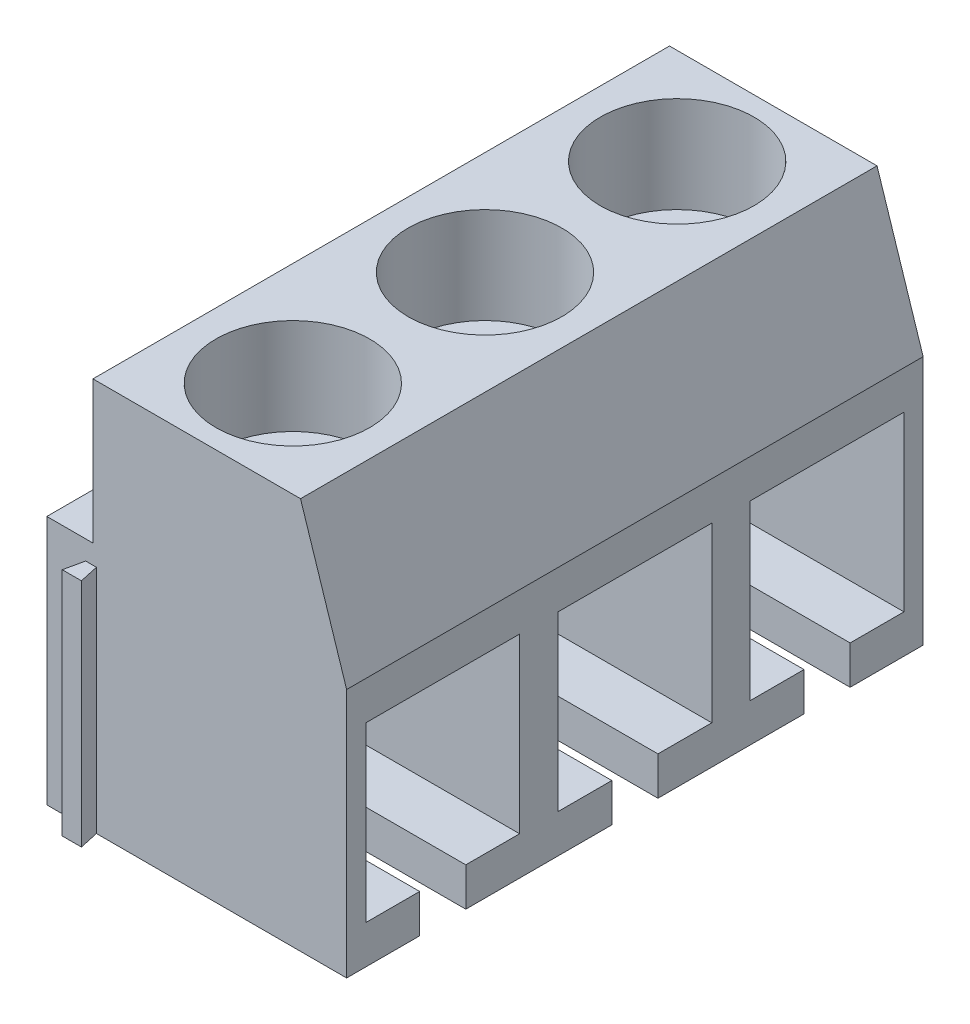
SolidWorks part; units mm, degrees
material "ABS"
ref_plane "Front Plane" through (0, 0, 0) normal (0, 0, 1) x (1, 0, 0)
ref_plane "Top Plane" through (0, 0, 0) normal (0, 1, 0) x (1, 0, 0)
ref_plane "Right Plane" through (0, 0, 0) normal (1, 0, 0) x (0, 0, -1)
sketch "Sketch1" plane through (0, 0, 0) normal (0, 0, 1) x (1, 0, 0)
  line L0 (-2.7, 5.1) -> (-2.7, 1.4)
  line L1 (-3.9, 5.1) -> (3.9, 5.1)
  line L2 (-3.9, 5.1) -> (-3.9, -5.1)
  line L3 (-3.9, -5.1) -> (3.9, -5.1)
  line L4 (3.9, 5.1) -> (3.9, -5.1)
  line L5 (-3.9, 5.1) -> (3.9, -5.1) construction
  line L6 (-3.9, -5.1) -> (3.9, 5.1) construction
  line L7 (-2.7, 1.4) -> (-3.9, 1.4)
  line L8 (3.9, 1.4) -> (2.7, 5.1)
  point P0 (0, 0)
  dimension "D1" = 10.2
  dimension "D2" = 7.8
  dimension "D3" = 1.2
  dimension "D4" = 6.5
  dimension "D5" = 1.2
extrude "Boss-Extrude1" add sketch "Sketch1" against normal blind 15 contours L4 L8 L1 L0 L7 L2 L3
sketch "Sketch3" plane through (0, 5.1, 0) normal (0, 1, 0) x (1, 0, 0)
  line L0 (-2, 2.5) -> (-2.7, 2.5) construction
  line L2 (0, 12.5) -> (0, 15) construction
  line L3 (-2.7, 15) -> (2.7, 15) construction
  line L4 (0, 2.5) -> (0, 0) construction
  line L5 (-2.7, 0) -> (2.7, 0) construction
  line L6 (-2.7, 15) -> (-2.7, 0) construction
  line L7 (2, 2.5) -> (2.7, 2.5) construction
  line L8 (2.7, 15) -> (2.7, 0) construction
  circle A0 centre (0, 2.5) radius 2
  circle A1 centre (0, 7.5) radius 2
  circle A2 centre (0, 12.5) radius 2
  dimension "D1" = 4
  dimension "D2" = 5
  dimension "D3" = 5
extrude "Cut-Extrude2" cut sketch "Sketch3" against normal blind 2.5
sketch "Sketch4" plane through (0, 2.6, 0) normal (0, 1, 0) x (1, 0, 0)
  circle A0 centre (0, 2.5) radius 1
  circle A1 centre (0, 7.5) radius 1
  circle A2 centre (0, 12.5) radius 1
  dimension "D1" = 2
extrude "Cut-Extrude3" cut sketch "Sketch4" against normal blind 3
sketch "Sketch2" plane through (3.9, 0, 0) normal (1, 0, 0) x (0, 0, -1)
  line L1 (0.5, -4.1) -> (4.5, -4.1)
  line L2 (0.5, 0.4) -> (4.5, 0.4)
  line L3 (0.5, 0.4) -> (0.5, -4.1)
  line L4 (0.5, -4.1) -> (4.5, -4.1)
  line L5 (4.5, 0.4) -> (4.5, -4.1)
  line L6 (2.5, 0.4) -> (2.5, -5.5283) construction
  line L10 (0, 1.4) -> (0, -5.1) construction
  line L11 (0.5, 1.4) -> (0.5, 0.4) construction
  line L12 (15, 1.4) -> (0, 1.4) construction
  line L16 (0.5, -4.1) -> (0.5, -5.1) construction
  line L17 (15, -5.1) -> (0, -5.1) construction
  dimension "D1" = 4
  dimension "D2" = 4.5
  dimension "D3" = 2.5
extrude "Cut-Extrude1" cut sketch "Sketch2" against normal blind 6 contours L5 L2 L3 L1
sketch "Sketch5" plane through (3.9, 0, 0) normal (1, 0, 0) x (0, 0, -1)
  line L0 (0.5, -4.1) -> (4.5, -4.1) construction
  line L1 (3.1, -4.1) -> (1.9, -4.1)
  line L2 (3.1, -4.1) -> (3.1, -6.1)
  line L3 (3.1, -6.1) -> (1.9, -6.1)
  line L4 (1.9, -4.1) -> (1.9, -6.1)
  line L5 (0.5, -4.1) -> (4.5, -4.1) construction
  point P6 (2.5, -4.1)
  point P9 (2.5, -4.1)
  dimension "D1" = 1.2
  dimension "D2" = 2
extrude "Cut-Extrude4" cut sketch "Sketch5" against normal blind 5.2
sketch "Sketch6" plane through (0, 0, 0) normal (0, 0, 1) x (1, 0, 0)
  line L0 (-3.9, -5.1) -> (3.9, -5.1) construction
  line L1 (-3, 0.9) -> (-2.5, 0.9)
  line L2 (-3, 0.9) -> (-3, -5.1)
  line L3 (-3, -5.1) -> (-2.5, -5.1)
  line L4 (-2.5, 0.9) -> (-2.5, -5.1)
  line L5 (-2.7, 1.4) -> (-3.9, 1.4) construction
  line L6 (-2.7, 5.1) -> (-2.7, 1.4) construction
  point P6 (-3.3, 1.4)
  dimension "D1" = 0.5
  dimension "D2" = 0.3
  dimension "D3" = 0.5
extrude "Boss-Extrude2" add sketch "Sketch6" along normal blind 0.5
sketch "Sketch7" plane through (0, 0, -15) normal (0, 0, -1) x (-1, 0, 0)
  line L0 (3.9, -5.1) -> (-3.9, -5.1) construction
  line L1 (2.5, 0.9) -> (3, 0.9)
  line L2 (2.5, 0.9) -> (2.5, -5.1)
  line L3 (2.5, -5.1) -> (3, -5.1)
  line L4 (3, 0.9) -> (3, -5.1)
  line L5 (2.7, 1.4) -> (3.9, 1.4) construction
  line L6 (2.7, 5.1) -> (2.7, 1.4) construction
  dimension "D1" = 0.5
  dimension "D2" = 0.3
  dimension "D3" = 0.5
extrude "Cut-Extrude5" cut sketch "Sketch7" against normal blind 0.5
pattern_linear "LPattern1" count 3 spacing 5 along (0, 0, -1) of "Cut-Extrude1", "Cut-Extrude4"
sketch "Sketch8" plane through (0, 0.9, 0) normal (0, 1, 0) x (1, 0, 0)
  line L0 (-3, -0.5) -> (-2.89, 0)
  line L1 (-2.5, 0) -> (-3, 0) construction
  line L2 (-2.89, 0) -> (-3, 0)
  line L3 (-2.7, 0) -> (-3.9, 0) construction
  line L4 (-3, 0) -> (-3, -0.5)
  line L5 (-2.5, -0.5) -> (-2.61, 0)
  line L6 (-2.61, 0) -> (-2.5, 0)
  line L7 (-2.7, 0) -> (2.7, 0) construction
  line L8 (-2.5, 0) -> (-2.5, -0.5)
  dimension "D1" = 0.11
extrude "Cut-Extrude6" cut sketch "Sketch8" against normal blind 10
sketch "Sketch9" plane through (0, -5.1, 0) normal (0, -1, 0) x (1, 0, 0)
  line L0 (-3, -14.5) -> (-2.89, -15)
  line L1 (-3, -15) -> (-2.5, -15) construction
  line L2 (-2.89, -15) -> (-3, -15)
  line L3 (-2.5, -14.5) -> (-2.61, -15)
  line L4 (-2.61, -15) -> (-2.5, -15)
  line L5 (-3, -14.5) -> (-3, -15)
  line L6 (-2.5, -14.5) -> (-2.5, -15)
  dimension "D1" = 0.11
extrude "Boss-Extrude3" add sketch "Sketch9" against normal up to surface (6 mm away) up to face at (-2.75, 0.9, -14.75)
